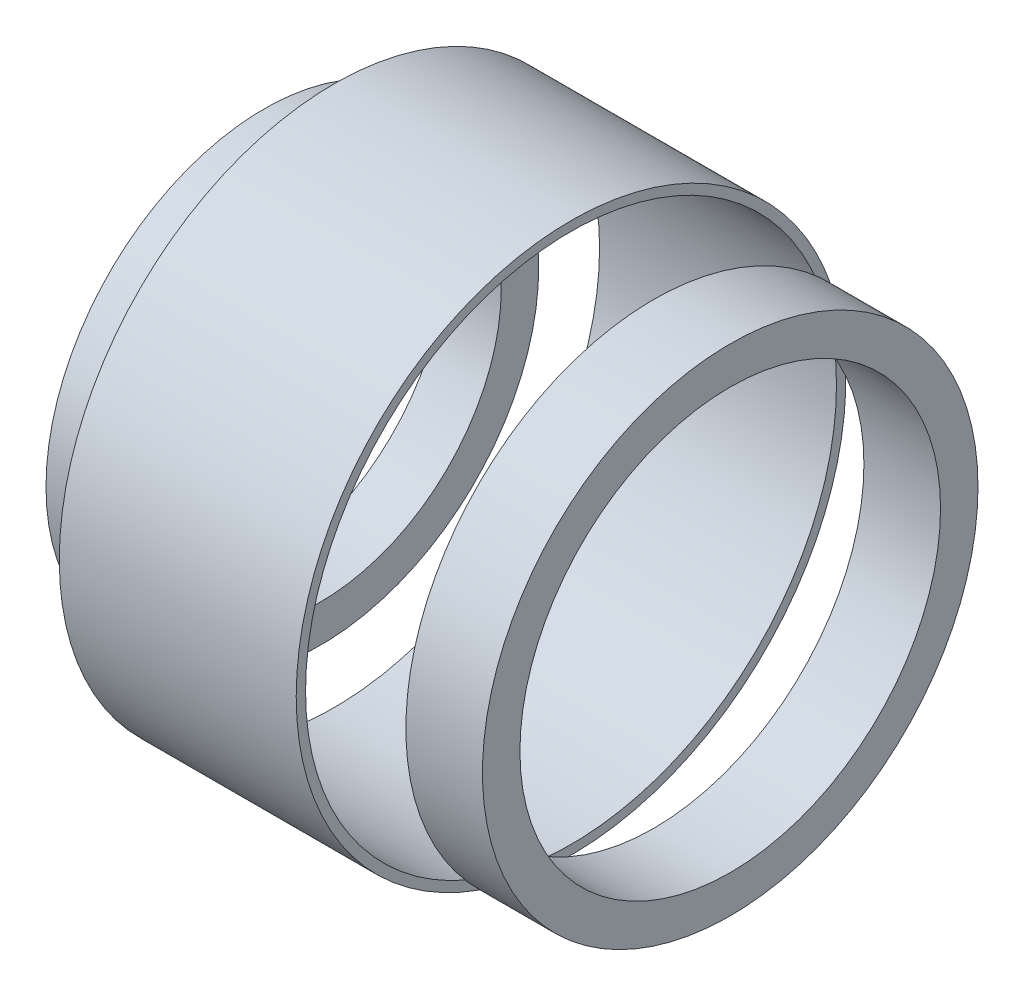
SolidWorks part; units mm, degrees
ref_plane "Front Plane" through (0, 0, 0) normal (0, 0, 1) x (1, 0, 0)
ref_plane "Top Plane" through (0, 0, 0) normal (0, 1, 0) x (1, 0, 0)
ref_plane "Right Plane" through (0, 0, 0) normal (1, 0, 0) x (0, 0, -1)
sketch "Sketch1" plane through (0, 0, 0) normal (0, 0, 1) x (1, 0, 0)
  line L0 (-61.9, 15) -> (-54.9, 15)
  line L1 (-54.9, -15) -> (-61.9, -15)
  line L2 (-54.9, -15) -> (-61.9, -15)
  line L3 (-61.9, 15) -> (-54.9, 15)
  line L4 (-48.4063, 15) -> (-41.4063, 15)
  line L5 (-41.4063, -15) -> (-48.4063, -15)
  line L6 (-41.4063, -15) -> (-48.4063, -15)
  line L7 (-48.4063, 15) -> (-41.4063, 15)
  line L8 (-89.0313, 12.5) -> (-82.0313, 12.5)
  line L9 (-82.0313, -12.5) -> (-89.0313, -12.5)
  line L10 (-82.0313, -12.5) -> (-89.0313, -12.5)
  line L11 (-89.0313, 12.5) -> (-82.0313, 12.5)
  line L12 (-100.7938, 12.5) -> (-93.7938, 12.5)
  line L13 (-93.7938, -12.5) -> (-100.7938, -12.5)
  line L14 (-93.7938, -12.5) -> (-100.7938, -12.5)
  line L15 (-100.7938, 12.5) -> (-93.7938, 12.5)
  line L16 (-61.9, -21) -> (-37.6125, -21)
  line L17 (-37.6125, 21) -> (-61.9, 21)
  line L18 (-37.6125, 21) -> (-61.9, 21)
  line L19 (-61.9, -21) -> (-37.6125, -21)
  line L20 (-104.5875, -18.5) -> (-82.0313, -18.5)
  line L21 (-82.0313, 18.5) -> (-104.5875, 18.5)
  line L22 (-82.0313, 18.5) -> (-104.5875, 18.5)
  line L23 (-104.5875, -18.5) -> (-82.0313, -18.5)
  line L24 (25.7162, 0) -> (-134.3819, 0) construction
  line L26 (-48.4063, 21) -> (-54.9, 21)
  line L27 (-48.4063, 21) -> (-48.4063, 17.825)
  line L28 (-48.4063, 17.825) -> (-54.9, 17.825)
  line L29 (-54.9, 21) -> (-54.9, 17.825)
  line L30 (-83.1375, 18.5) -> (-87.9, 18.5)
  line L31 (-83.1375, 18.5) -> (-83.1375, 15.325)
  line L32 (-83.1375, 15.325) -> (-87.9, 15.325)
  line L33 (-87.9, 18.5) -> (-87.9, 15.325)
  dimension "D1" = 3.175
revolve "Revolve1" add sketch "Sketch1" angle 360 about L24
ref_axis "Axis1" through (-121.0609, 0, 0) along (1, 0, 0)
sketch "Sketch2" plane through (0, 0, 0) normal (0, 1, 0) x (1, 0, 0)
  line L0 (-81.9812, 29) -> (-81.9812, -29) construction
  line L1 (-61.9, 23.2938) -> (-81.9812, 23.2938)
  line L2 (-61.9, 23.2938) -> (-61.9, 22.5)
  line L3 (-61.9, 22.5) -> (-81.9812, 22.5)
  line L4 (-81.9812, 23.2938) -> (-81.9812, 22.5)
  dimension "D1" = 0.7937
revolve "Revolve2" add sketch "Sketch2" angle 360 about axis through (-121.0609, 0, 0) along (1, 0, 0)
